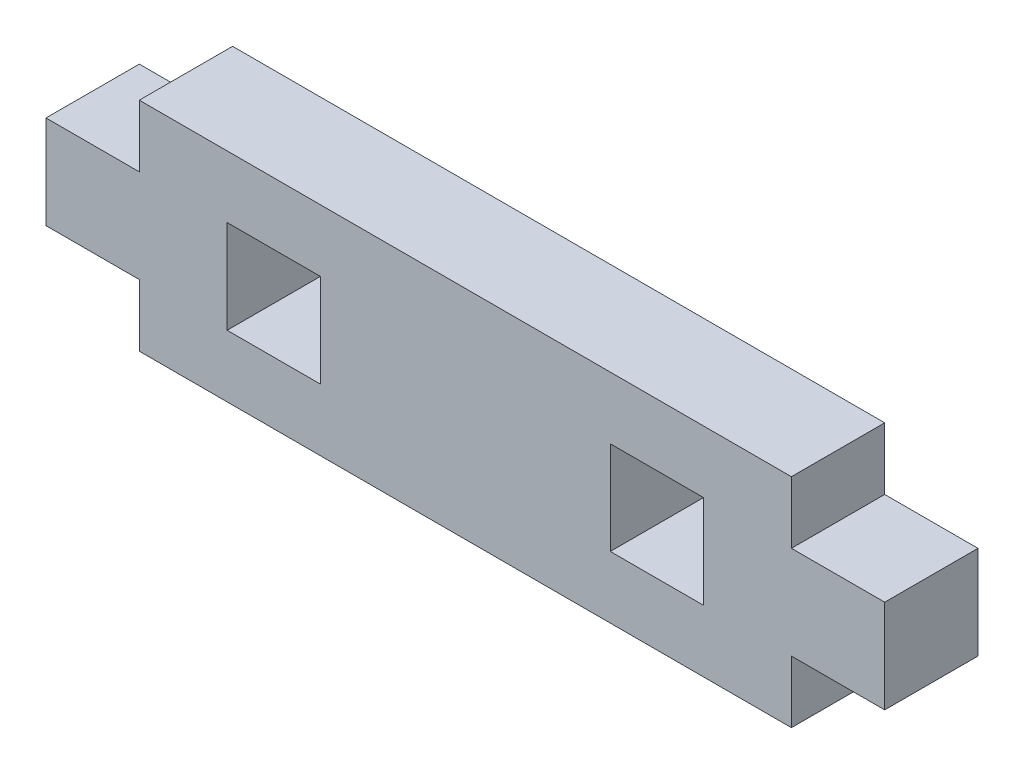
SolidWorks part; units mm, degrees
ref_plane "Front Plane" through (0, 0, 0) normal (0, 0, 1) x (1, 0, 0)
ref_plane "Top Plane" through (0, 0, 0) normal (0, 1, 0) x (1, 0, 0)
ref_plane "Right Plane" through (0, 0, 0) normal (1, 0, 0) x (0, 0, -1)
sketch "Sketch2" plane through (0, 0, 0) normal (0, 0, 1) x (1, 0, 0)
  line L0 (0, 3.425) -> (0, 8.575)
  line L1 (0, -55) -> (0, 55) construction
  line L2 (0, 8.575) -> (5.15, 8.575)
  line L3 (5.15, 8.575) -> (5.15, 12)
  line L4 (55, 0) -> (-55, 0) construction
  line L5 (5.15, 0) -> (41.15, 0)
  line L6 (41.15, 8.575) -> (41.15, 12)
  line L7 (41.15, 8.575) -> (46.3, 8.575)
  line L8 (46.3, 8.575) -> (46.3, 3.425)
  line L9 (46.3, 3.425) -> (41.15, 3.425)
  line L10 (41.15, 0) -> (41.15, 3.425)
  line L11 (41.15, 12) -> (5.15, 12)
  line L12 (5.15, 0) -> (5.15, 3.425)
  line L13 (5.15, 3.425) -> (0, 3.425)
  dimension "D1" = 36
  dimension "D2" = 5.15
  dimension "D3" = 12
  dimension "D4" = 5.15
extrude "Boss-Extrude1" add sketch "Sketch2" along normal blind 5.15
sketch "Sketch3" plane through (0, 0, 5.15) normal (0, 0, 1) x (1, 0, 0)
  line L0 (13.0469, 8.575) -> (13.0469, 12) construction
  line L1 (41.15, 12) -> (5.15, 12) construction
  line L2 (10, 8.575) -> (10, 3.425)
  line L3 (13.0469, 3.425) -> (13.0469, 0) construction
  line L4 (15.15, 3.425) -> (10, 3.425)
  line L5 (31.15, 8.575) -> (36.3, 8.575)
  line L6 (31.15, 8.575) -> (31.15, 3.425)
  line L7 (31.15, 3.425) -> (36.3, 3.425)
  line L8 (36.3, 8.575) -> (36.3, 3.425)
  line L9 (15.15, 8.575) -> (15.15, 3.425)
  line L10 (15.15, 8.575) -> (10, 8.575)
  line L11 (55, 0) -> (-55, 0) construction
  line L12 (23.15, 12) -> (23.15, -3.9207) construction
  dimension "D1" = 5.15
  dimension "D2" = 5.15
  dimension "D3" = 16
extrude "Cut-Extrude1" cut sketch "Sketch3" against normal through all
